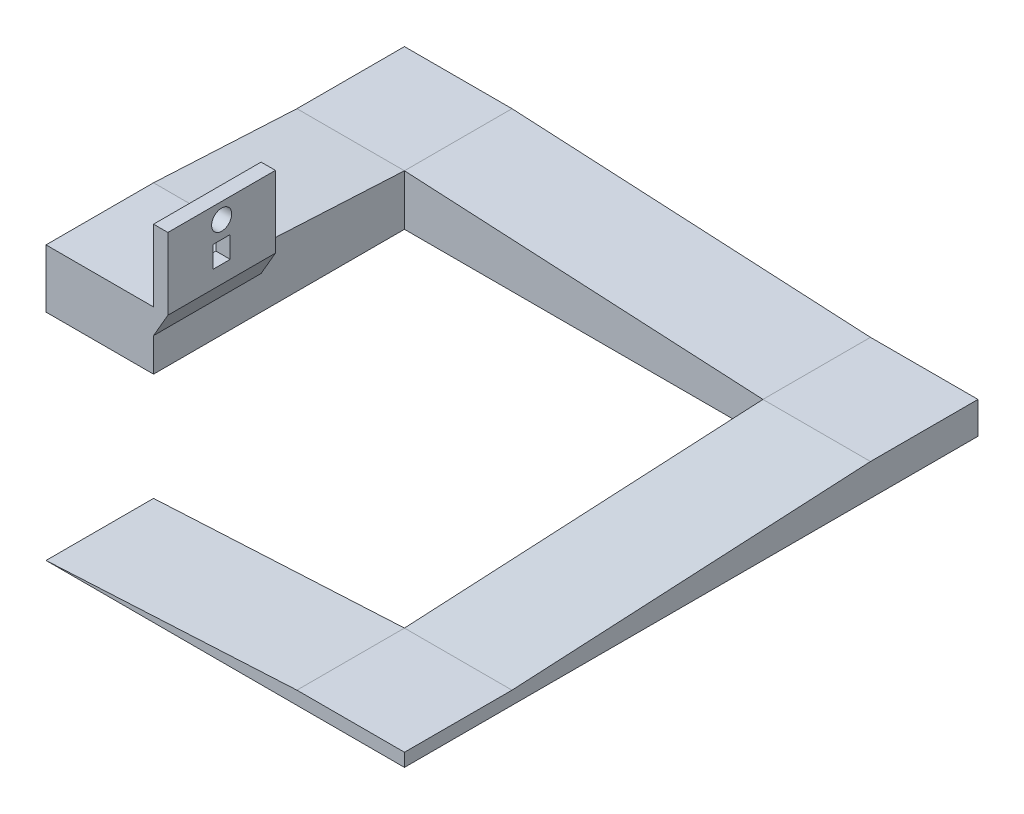
SolidWorks part; units mm, degrees
ref_plane "Front Plane" through (0, 0, 0) normal (0, 0, 1) x (1, 0, 0)
ref_plane "Top Plane" through (0, 0, 0) normal (0, 1, 0) x (1, 0, 0)
ref_plane "Right Plane" through (0, 0, 0) normal (1, 0, 0) x (0, 0, -1)
sketch "Sketch1" plane through (0, 0, 0) normal (0, 0, 1) x (1, 0, 0)
  line L0 (0, 0) -> (44.45, 2.3295)
  line L2 (63.5, 0) -> (0, 0)
  line L3 (44.45, 2.3295) -> (63.5, 2.3295)
  line L4 (63.5, 2.3295) -> (63.5, 0)
  dimension "D1" = 3
  dimension "D2" = 63.5
  dimension "D3" = 19.05
extrude "Boss-Extrude1" add sketch "Sketch1" along normal blind 19.05 contours L2 L0 L3 L4
sketch "Sketch2" plane through (63.5, 0, 0) normal (1, 0, 0) x (0, 0, -1)
  line L0 (0, 0) -> (0, 2.3295)
  line L1 (0, 2.3295) -> (63.5, 5.6574)
  line L2 (63.5, 5.6574) -> (82.55, 5.6574)
  line L3 (82.55, 5.6574) -> (82.55, 0)
  line L4 (82.55, 0) -> (0, 0)
  dimension "D1" = 3
  dimension "D2" = 19.05
  dimension "D3" = 82.55
extrude "Boss-Extrude2" add sketch "Sketch2" against normal blind 19.05
sketch "Sketch3" plane through (0, 0, -82.55) normal (0, 0, -1) x (-1, 0, 0)
  line L0 (-44.45, 0) -> (-44.45, 5.6574)
  line L1 (-44.45, 5.6574) -> (19.05, 8.9853)
  line L2 (19.05, 8.9853) -> (38.1, 8.9853)
  line L3 (38.1, 8.9853) -> (38.1, 0)
  line L4 (38.1, 0) -> (-44.45, 0)
  dimension "D1" = 3
  dimension "D2" = 19.05
  dimension "D3" = 82.55
extrude "Boss-Extrude3" add sketch "Sketch3" against normal blind 19.05
sketch "Sketch4" plane through (-38.1, 0, 0) normal (-1, 0, 0) x (0, 0, 1)
  line L0 (-63.5, 8.9853) -> (-38.1, 10.3165)
  line L1 (-38.1, 10.3165) -> (-19.05, 10.3165)
  line L2 (-19.05, 10.3165) -> (-19.05, 0)
  line L3 (-19.05, 0) -> (-63.5, 0)
  line L4 (-63.5, 0) -> (-63.5, 8.9853)
  dimension "D1" = 3
  dimension "D2" = 19.05
  dimension "D3" = 44.45
extrude "Boss-Extrude4" add sketch "Sketch4" against normal blind 19.05
sketch "Sketch13" plane through (0, 0, -19.05) normal (0, 0, 1) x (1, 0, 0)
  line L0 (-19.05, 5.9171) -> (-19.05, 23.0165)
  line L1 (-19.05, 23.0165) -> (-16.51, 23.0165)
  line L2 (-16.51, 23.0165) -> (-16.51, 10.3165)
  line L3 (-16.51, 10.3165) -> (-19.05, 5.9171)
  line L4 (-19.05, 8.9853) -> (-19.05, 0) construction
  line L5 (-19.05, 10.3165) -> (-38.1, 10.3165) construction
  dimension "D1" = 30
  dimension "D2" = 12.7
  dimension "D3" = 2.54
  dimension "D4" = 12.7
extrude "Boss-Extrude13" add sketch "Sketch13" against normal blind 19.05
sketch "Sketch14" plane through (-19.05, 0, 0) normal (-1, 0, 0) x (0, 0, 1)
  line L0 (-38.1, 23.0165) -> (-19.05, 23.0165) construction
  line L1 (-30.099, 17.1745) -> (-27.051, 17.1745)
  line L2 (-30.099, 17.1745) -> (-30.099, 13.3645)
  line L3 (-30.099, 13.3645) -> (-27.051, 13.3645)
  line L4 (-27.051, 17.1745) -> (-27.051, 13.3645)
  line L5 (-38.1, 23.0165) -> (-19.05, 23.0165) construction
  circle A0 centre (-28.575, 20.2225) radius 1.778
  point P6 (-28.575, 17.1745)
  point P7 (-28.575, 22.0005)
  point P12 (-28.575, 23.0165)
  dimension "D1" = 3.556
  dimension "D2" = 3.81
  dimension "D3" = 3.048
  dimension "D4" = 1.016
  dimension "D5" = 5.842
extrude "Cut-Extrude1" cut sketch "Sketch14" against normal up to next
